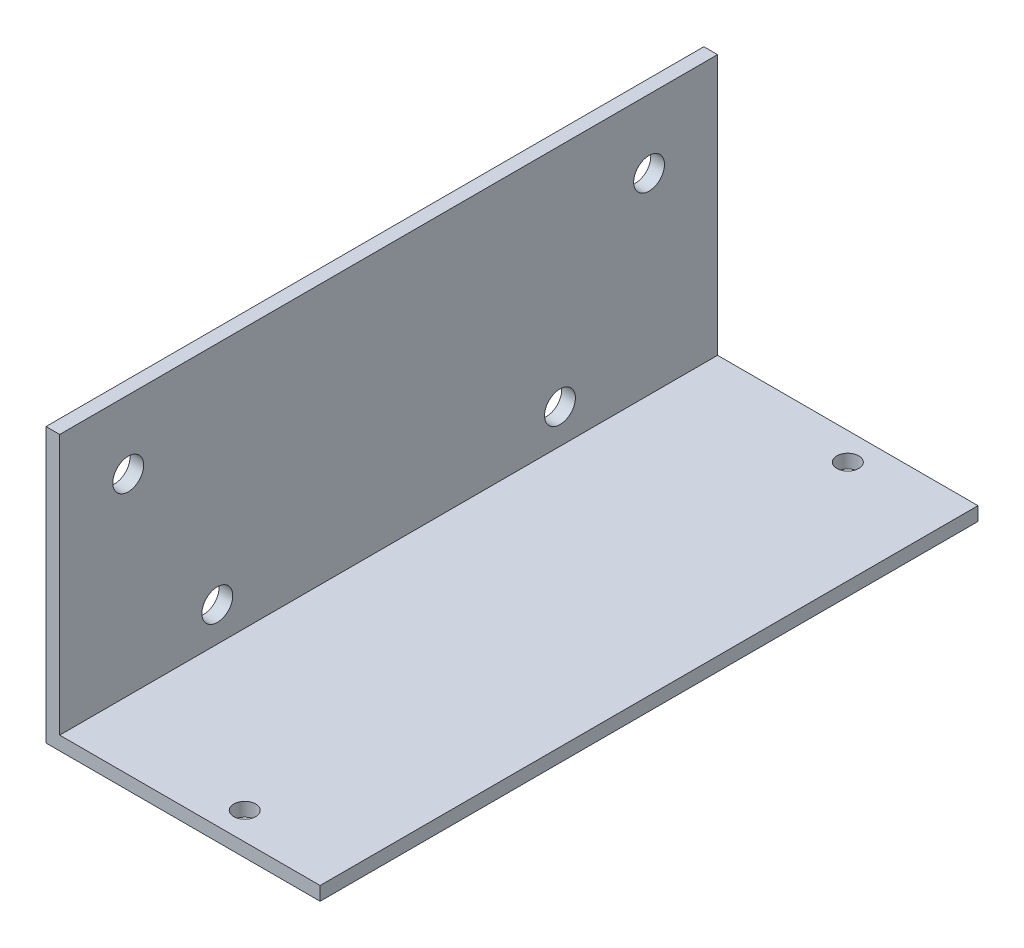
SolidWorks part; units mm, degrees
material "1060 Сплав"
ref_plane "Спереди" through (0, 0, 0) normal (0, 0, 1) x (1, 0, 0)
ref_plane "Сверху" through (0, 0, 0) normal (0, 1, 0) x (1, 0, 0)
ref_plane "Справа" through (0, 0, 0) normal (1, 0, 0) x (0, 0, -1)
sketch "Эскиз1" plane through (0, 0, 0) normal (0, 0, 1) x (1, 0, 0)
  line L0 (0, 0) -> (40, 0)
  line L1 (40, 0) -> (40, 2)
  line L2 (40, 2) -> (2, 2)
  line L3 (2, 2) -> (2, 40)
  line L4 (2, 40) -> (0, 40)
  line L5 (0, 40) -> (0, 0)
  dimension "D1" = 40
  dimension "D2" = 2
  dimension "D3" = 40
extrude "Бобышка-Вытянуть1" add sketch "Эскиз1" along normal blind 96
sketch "Эскиз2" plane through (0, 0, 0) normal (0, -1, 0) x (1, 0, 0)
  line L0 (40, 96) -> (40, 0) construction
  line L3 (0, 0) -> (40, 0) construction
  line L4 (25, 4) -> (25, 96) construction
  line L5 (0, 96) -> (40, 96) construction
  circle A1 centre (25, 92) radius 1.6
  circle A2 centre (25, 4) radius 1.6
  dimension "D1" = 15
  dimension "D2" = 4
  dimension "D3" = 3.2
  dimension "D4" = 3.2
  dimension "D5" = 4
extrude "Вырез-Вытянуть1" cut sketch "Эскиз2" against normal through all
sketch "Эскиз3" plane through (0, 0, 0) normal (-1, 0, 0) x (0, 0, 1)
  line L0 (0, 30) -> (96, 30) construction
  line L1 (96, 40) -> (0, 40) construction
  line L3 (0, 40) -> (0, 0) construction
  line L4 (96, 40) -> (96, 0) construction
  line L5 (96, 7) -> (0, 7) construction
  line L6 (96, 0) -> (0, 0) construction
  circle A0 centre (10, 30) radius 2.25
  circle A1 centre (86, 30) radius 2.25
  circle A2 centre (73, 7) radius 2.25
  circle A3 centre (23, 7) radius 2.25
  point P16 (48, 7)
  dimension "D1" = 4.5
  dimension "D2" = 10
  dimension "D3" = 10
  dimension "D4" = 10
  dimension "D6" = 4.5
  dimension "D7" = 50
  dimension "D8" = 25
  dimension "D5" = 7
extrude "Вырез-Вытянуть2" cut sketch "Эскиз3" against normal through all
equation "\"3ю2\"=3.4952"
